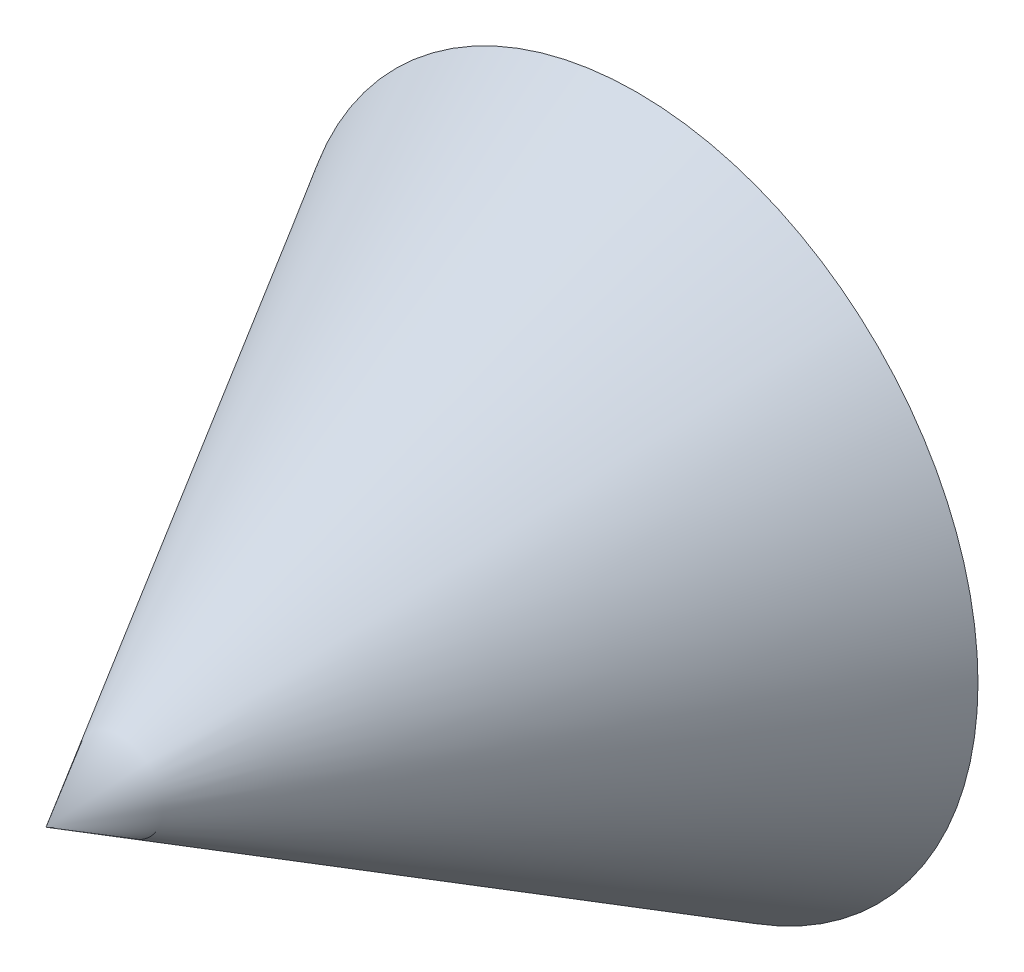
SolidWorks part; units mm, degrees
ref_plane "Front Plane" through (0, 0, 0) normal (0, 0, 1) x (1, 0, 0)
ref_plane "Top Plane" through (0, 0, 0) normal (0, 1, 0) x (1, 0, 0)
ref_plane "Right Plane" through (0, 0, 0) normal (1, 0, 0) x (0, 0, -1)
sketch "Sketch1" plane through (0, 0, 0) normal (0, 1, 0) x (1, 0, 0)
  line L0 (0, 0) -> (0, 7.55)
  line L1 (0, 7.55) -> (-4.3563, 7.55)
  line L2 (-4.3563, 7.55) -> (0, 0)
  dimension "D1" = 4.3563
  dimension "D2" = 7.55
revolve "Revolve1" add sketch "Sketch1" angle 360 about L0
